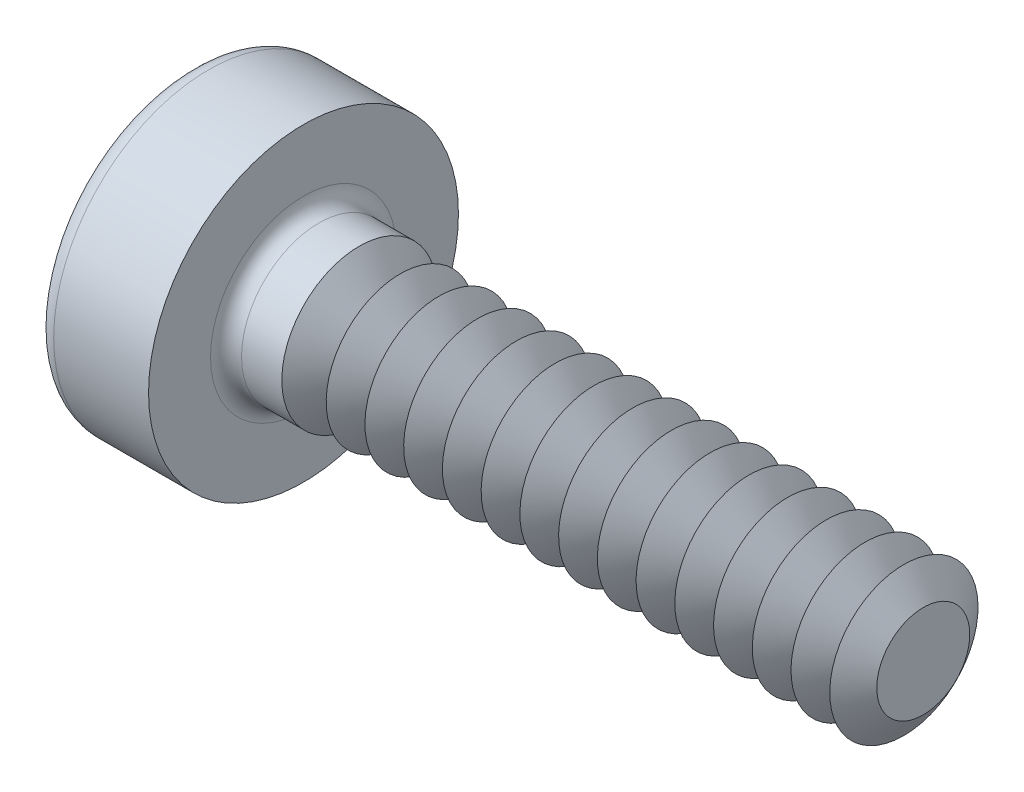
SolidWorks part; units mm, degrees
ref_plane "Plane1" through (0, 0, 0) normal (0, 0, 1) x (1, 0, 0)
ref_plane "Plane2" through (0, 0, 0) normal (0, 1, 0) x (1, 0, 0)
ref_plane "Plane3" through (0, 0, 0) normal (1, 0, 0) x (0, 0, -1)
sketch "BodySke" plane through (0, 0, 0) normal (0, 0, 1) x (1, 0, 0)
  line L0 (1, 0.5) -> (1, 1)
  line L1 (1.125, 6.35) -> (1.125, -3.175) construction
  line L2 (-25.4, 0) -> (127, 0) construction
  line L3 (5, 0) -> (0, 0)
  line L4 (1, 0.5) -> (5, 0.5)
  line L5 (5, 0.5) -> (5, 0)
  line L6 (0.3878, 1) -> (1, 1)
  line L8 (1, 6.35) -> (1, -3.175) construction
  arc A0 (0.2881, 0.9468) -> (0, 0) centre (1.7, 0) ccw
  arc A2 (0.2881, 0.9468) -> (0.3878, 1) centre (0.3878, 0.88) cw
  dimension "Head_crown_rad" = 1.7
  dimension "Head_fillet_rad" = 0.12
  dimension "Length" = 4
  dimension "Head_ht" = 1
  dimension "Head_dia" = 2
  dimension "Advance" = 0.25
  dimension "Thread_nom" = 4
  dimension "Diameter" = 1
revolve "Base-Revolve" add sketch "BodySke"
cosmetic thread "ThreadCosmetic" [suppressed]
fillet "Fillet1" radius 0.1 1 edges at (1, 0, 0.5)
sketch "Sketch3" plane through (0, 0, 0) normal (1, 0, 0) x (0, 0, -1)
  line L0 (0.24, -0.8) -> (-0.24, -0.8)
  line L1 (0.24, -0.8) -> (0.24, 0.8)
  line L2 (-0.24, 0.8) -> (0.24, 0.8)
  line L3 (-0.24, 0.8) -> (-0.24, -0.8)
  dimension "Cross_dia" = 1.6
  dimension "D1" = 0.8
  dimension "Cross_width" = 0.48
  dimension "D2" = 0.24
ref_plane "Plane4" through (0.5, 0, 0) normal (1, 0, 0) x (0, 0, -1)
sketch "Sketch4" plane through (0.5, 0, 0) normal (1, 0, 0) x (0, 0, -1)
  line L0 (0.24, -0.5507) -> (-0.24, -0.5507)
  line L1 (0.24, -0.5507) -> (0.24, 0.5507)
  line L2 (-0.24, 0.5507) -> (0.24, 0.5507)
  line L3 (-0.24, 0.5507) -> (-0.24, -0.5507)
  dimension "D1" = 0.48
  dimension "D2" = 1.1014
  dimension "D3" = 0.24
  dimension "D4" = 0.5507
loft "Recess" cut profiles "Sketch3", "Sketch4"
pattern_circular "RecPat" count 2 every 90 about axis through (0, 0, 0) along (1, 0, 0) of "Recess"
sketch "RecCorSke" plane through (0, 0, 0) normal (0, 0, 1) x (1, 0, 0)
  line L0 (-3.175, 0) -> (15.875, 0) construction
  line L1 (-25.4, 0) -> (127, 0) construction
  line L2 (0, 0) -> (0, 0.3905)
  line L3 (0, 0.3905) -> (0.5, 0.3555)
  line L4 (0.5, 0.3555) -> (0.6155, 0)
  line L5 (0.6155, 0) -> (0, 0)
  dimension "Diameter" = 0.711
  dimension "Depth" = 0.5
  dimension "Draft_angle" = 4
  dimension "Bottom_angle" = 18
revolve "RecessCore" cut sketch "RecCorSke" angle 360 about L0
sketch "ThdSchSke" plane through (0, 0, 0) normal (0, 0, 1) x (1, 0, 0)
  line L0 (1.5, -0.3) -> (1.36, -0.5)
  line L1 (1.5, -0.3) -> (1.64, -0.5)
  line L2 (1.64, -0.5) -> (1.64, -0.625)
  line L3 (-3.175, 0) -> (5.1513, 0) construction
  line L5 (1.64, -0.625) -> (1.36, -0.625)
  line L6 (1.36, -0.625) -> (1.36, -0.5)
  dimension "Diameter" = 1
  dimension "SideAngle" = 55
  dimension "VeeAngle" = 70
  dimension "Thread_minor" = 0.6
  dimension "Overcut" = 1.25
  dimension "Start" = 1.5
revolve "ThreadSchematic" cut sketch "ThdSchSke" angle 360 about L3
pattern_linear "ThdSchPat" count 15 spacing 0.25 along (1, 0, 0) of "ThreadSchematic"
equation "\"D1@Sketch3\" = \"Cross_dia@Sketch3\" / 2"
equation "\"D2@Sketch3\" = \"Cross_width@Sketch3\" / 2"
equation "\"Depth@RecCorSke\" = \"Cross_depth@Plane4\""
equation "\"D1@Sketch4\" = \"Cross_width@Sketch3\""
equation "\"D2@Sketch4\" = \"Cross_dia@Sketch3\" - 2.0 * \"Cross_depth@Plane4\" * tan(26.5  * 0.017453292)"
equation "\"D3@Sketch4\" = \"D1@Sketch4\" / 2"
equation "\"D4@Sketch4\" = \"D2@Sketch4\" / 2"
equation "\"Thread_length@ThreadCosmetic\" = ((sgn( (\"Length@BodySke\" - \"Advance@BodySke\" * 2.0 ) - \"Thread_nom@BodySke\" )-1)*( (\"Length@BodySke\" - \"Advance@BodySke\" * 2.0 ) - \"Thread_nom@BodySke\" ))/-2+ \"Thread_nom@BodySke\""
equation "\"Thread_minor@ThdSchSke\" = \"Thread_minor@ThreadCosmetic\""
equation "\"Diameter@ThdSchSke\" = \"Diameter@BodySke\""
equation "\"Overcut@ThdSchSke\" = \"Diameter@BodySke\" * 1.25"
equation "\"Start@ThdSchSke\" = \"Head_ht@BodySke\" + \"Length@BodySke\" - \"Thread_length@ThreadCosmetic\"  '---Non-countersunk---"
equation "\"Num_threads@ThdSchPat\" = int( \"Thread_length@ThreadCosmetic\" / \"Advance@BodySke\" + 0.999 )  + 1"
equation "\"Advance@ThdSchPat\" = \"Thread_length@ThreadCosmetic\" /  (\"Num_threads@ThdSchPat\" - 1) 'relax it"
